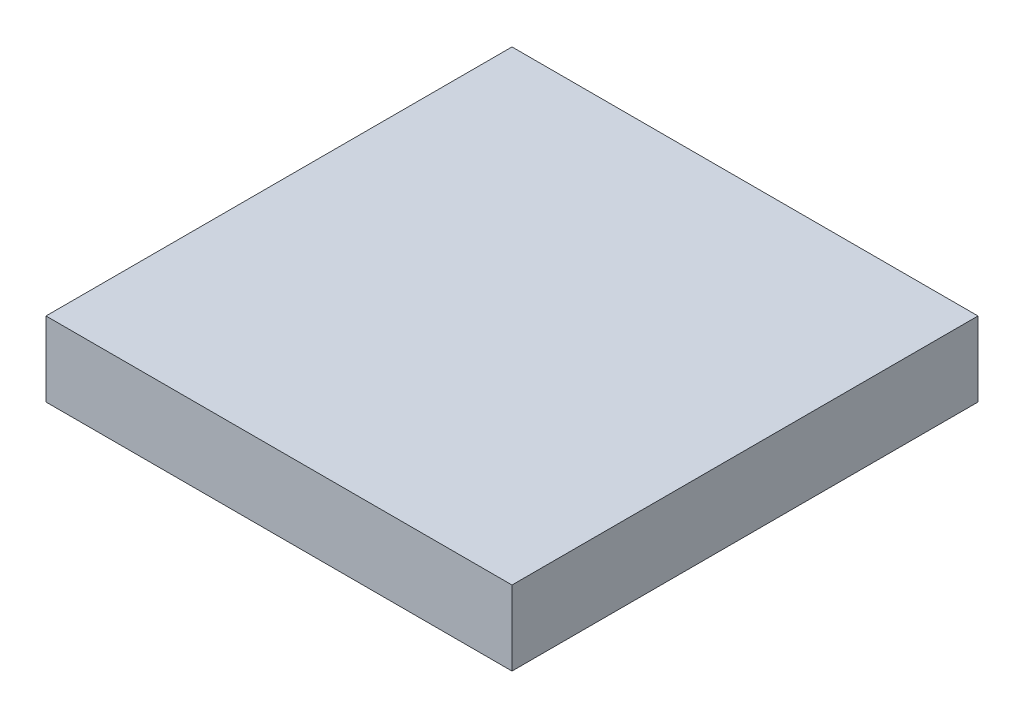
SolidWorks part; units mm, degrees
ref_plane "Front Plane" through (0, 0, 0) normal (0, 0, 1) x (1, 0, 0)
ref_plane "Top Plane" through (0, 0, 0) normal (0, 1, 0) x (1, 0, 0)
ref_plane "Right Plane" through (0, 0, 0) normal (1, 0, 0) x (0, 0, -1)
sketch "Sketch1" plane through (0, 0, 0) normal (0, 1, 0) x (1, 0, 0)
  line L0 (0, 0) -> (18.6879, 0) construction
  line L1 (0, 0) -> (0, -14.4281) construction
  line L3 (-1.25, 1.25) -> (1.25, 1.25)
  line L4 (-1.25, 1.25) -> (-1.25, -1.25)
  line L5 (-1.25, -1.25) -> (1.25, -1.25)
  line L6 (1.25, 1.25) -> (1.25, -1.25)
  dimension "D1" = 2.5
  dimension "D2" = 2.5
extrude "Boss-Extrude1" add sketch "Sketch1" along normal blind 0.4
